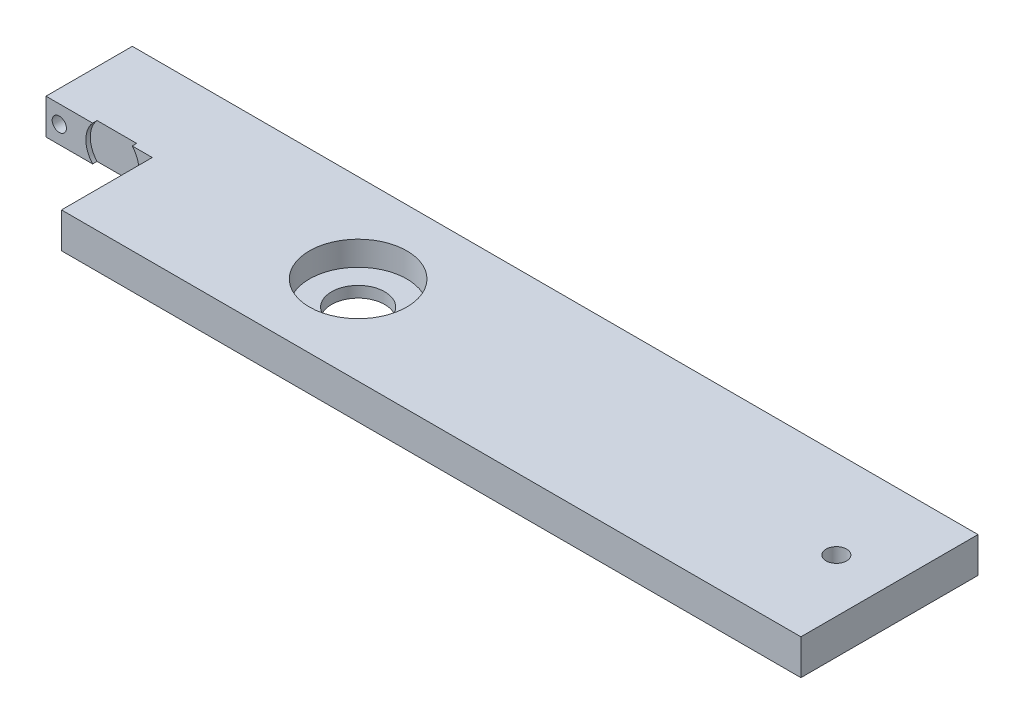
SolidWorks part; units mm, degrees
material "6061-T6 (SS)"
ref_plane "Front Plane" through (0, 0, 0) normal (0, 0, 1) x (1, 0, 0)
ref_plane "Top Plane" through (0, 0, 0) normal (0, 1, 0) x (1, 0, 0)
ref_plane "Right Plane" through (0, 0, 0) normal (1, 0, 0) x (0, 0, -1)
sketch "Sketch1" plane through (0, 0, 0) normal (0, 1, 0) x (1, 0, 0)
  line L0 (-114.3, 31.75) -> (-114.3, 0.7938) construction
  line L1 (-112.7125, 31.75) -> (190.5, 31.75)
  line L2 (-190.5, 31.75) -> (-190.5, -31.75) construction
  line L3 (-74.6125, -31.75) -> (190.5, -31.75)
  line L4 (190.5, 31.75) -> (190.5, -31.75)
  line L5 (-190.5, 31.75) -> (190.5, -31.75) construction
  line L6 (-190.5, -31.75) -> (190.5, 31.75) construction
  line L7 (-112.7125, 0.7938) -> (-76.2, 0.7938)
  line L8 (-76.2, 0.7938) -> (-76.2, -31.75) construction
  line L9 (-190.5, 31.75) -> (-114.3, 31.75) construction
  line L10 (-190.5, -31.75) -> (-76.2, -31.75) construction
  line L11 (-112.7125, 31.75) -> (-112.7125, 0.7938)
  line L12 (-74.6125, -31.75) -> (-74.6125, 0.7938)
  line L13 (-74.6125, 0.7938) -> (-76.2, 0.7938)
  line L14 (-114.3, 0.7938) -> (-112.7125, 0.7938) construction
  line L15 (-114.3, 31.75) -> (-112.7125, 31.75) construction
  line L16 (-76.2, -31.75) -> (-74.6125, -31.75) construction
  point P0 (0, 0)
  dimension "D1" = 381
  dimension "D2" = 63.5
  dimension "D3" = 0.7937
  dimension "D4" = 38.1
  dimension "D5" = 76.2
  dimension "D6" = 1.5875
  dimension "D7" = 1.5875
extrude "Boss-Extrude1" add sketch "Sketch1" along normal blind 12.7
sketch "Sketch2" plane through (0, 12.7, 0) normal (0, 1, 0) x (1, 0, 0)
  circle A0 centre (0, 0) radius 17.4625
  dimension "D1" = 34.925
extrude "Cut-Extrude1" cut sketch "Sketch2" against normal blind 8.7312
sketch "Sketch4" plane through (0, 12.7, 0) normal (0, 1, 0) x (1, 0, 0)
  line L2 (171.45, 0) -> (190.5, 0) construction
  line L3 (190.5, -31.75) -> (190.5, 31.75) construction
  circle A1 centre (171.45, 0) radius 3.683
  dimension "D1" = 7.366
  dimension "D2" = 19.05
extrude "Cut-Extrude3" cut sketch "Sketch4" against normal through all
hole_wizard "#10 Clearance Hole1" positions "Sketch5" profile "Sketch6" hole size "#10" standard "ANSI Inch" end condition through all
sketch "Sketch5" plane through (0, 0, -31.75) normal (0, 0, -1) x (-1, 0, 0)
  line L1 (114.3, 0) -> (107.95, 6.35) construction
  line L2 (107.95, 6.35) -> (114.3, 12.7) construction
  line L3 (114.3, -987.3) -> (114.3, 49012.7) construction
  line L4 (112.7125, 12.7) -> (112.7125, 0) construction
  line L5 (-190.5, 12.7) -> (112.7125, 12.7) construction
  line L6 (-190.5, 0) -> (112.7125, 0) construction
  point P0 (107.95, 6.35)
  dimension "D1" = 6.35
  dimension "D2" = 1.5875
sketch "Sketch6" plane through (-107.95, 6.35, -31.75) normal (1, 0, 0) x (0, 1, 0)
  line L0 (0, 0) -> (0, 63.5)
  line L1 (0, 63.5) -> (2.5527, 63.5)
  line L2 (2.5527, 63.5) -> (2.5527, 0)
  line L5 (2.5527, 0) -> (0, 0)
  line L11 (0, -6.35) -> (0, 107.95) construction
  dimension "Thru Hole Dia." = 5.1054
  dimension "Thru Hole Depth" = 63.5
sketch "Sketch7" plane through (0, 0, -0.7938) normal (0, 0, 1) x (1, 0, 0)
  line L0 (-88.9, 12.7) -> (-88.9, 6.35) construction
  line L1 (-112.7125, 12.7) -> (-74.6125, 12.7) construction
  line L2 (-88.9, 6.35) -> (-88.9, 0) construction
  line L3 (-112.7125, 0) -> (-74.6125, 0) construction
  line L5 (-76.2, -995.5919) -> (-76.2, 49004.4081) construction
  line L6 (-74.6125, 12.7) -> (-74.6125, 0) construction
  circle A0 centre (-88.9, 6.35) radius 9.525
  dimension "D1" = 19.05
  dimension "D2" = 12.7
  dimension "D3" = 1.5875
extrude "Cut-Extrude4" cut sketch "Sketch7" against normal blind 1.5875
sketch "Sketch8" plane through (0, 3.9688, 0) normal (0, 1, 0) x (1, 0, 0)
  circle A0 centre (0, 0) radius 9.525
  dimension "D1" = 19.05
extrude "Cut-Extrude5" cut sketch "Sketch8" against normal through all contours A0
